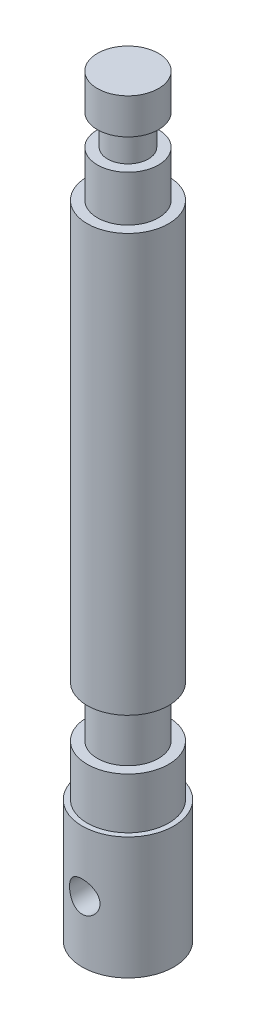
SolidWorks part; units mm, degrees
ref_plane "Front Plane" through (0, 0, 0) normal (0, 0, 1) x (1, 0, 0)
ref_plane "Top Plane" through (0, 0, 0) normal (0, 1, 0) x (1, 0, 0)
ref_plane "Right Plane" through (0, 0, 0) normal (1, 0, 0) x (0, 0, -1)
sketch "Sketch1" plane through (0, 0, 0) normal (0, 1, 0) x (1, 0, 0)
  circle A0 centre (0, 0) radius 9
  dimension "D1" = 18
extrude "Boss-Extrude1" add sketch "Sketch1" along normal blind 24
sketch "Sketch2" plane through (0, 24, 0) normal (0, 1, 0) x (1, 0, 0)
  circle A0 centre (0, 0) radius 8
  dimension "D1" = 16
extrude "Boss-Extrude2" add sketch "Sketch2" along normal blind 10
sketch "Sketch3" plane through (0, 34, 0) normal (0, 1, 0) x (1, 0, 0)
  circle A0 centre (0, 0) radius 6
  dimension "D1" = 12
extrude "Boss-Extrude3" add sketch "Sketch3" along normal blind 10
sketch "Sketch4" plane through (0, 44, 0) normal (0, 1, 0) x (1, 0, 0)
  circle A0 centre (0, 0) radius 8
  dimension "D1" = 16
extrude "Boss-Extrude4" add sketch "Sketch4" along normal blind 82
sketch "Sketch5" plane through (0, 126, 0) normal (0, 1, 0) x (1, 0, 0)
  circle A0 centre (0, 0) radius 6
  dimension "D1" = 12
extrude "Boss-Extrude5" add sketch "Sketch5" along normal blind 9
sketch "Sketch6" plane through (0, 135, 0) normal (0, 1, 0) x (1, 0, 0)
  circle A0 centre (0, 0) radius 4
  dimension "D1" = 8
extrude "Boss-Extrude6" add sketch "Sketch6" along normal blind 6
sketch "Sketch7" plane through (0, 141, 0) normal (0, 1, 0) x (1, 0, 0)
  circle A0 centre (0, 0) radius 6
  dimension "D1" = 12
extrude "Boss-Extrude7" add sketch "Sketch7" along normal blind 7
sketch "Sketch8" plane through (0, 0, 0) normal (0, 0, 1) x (1, 0, 0)
  line L0 (-9, 0) -> (9, 0) construction
  circle A0 centre (0, 12) radius 3
  point P4 (0, 0)
  point P6 (0, 0)
  dimension "D1" = 12
  dimension "D2" = 6
extrude "Cut-Extrude1" cut sketch "Sketch8" against normal through all both and the other way through all
